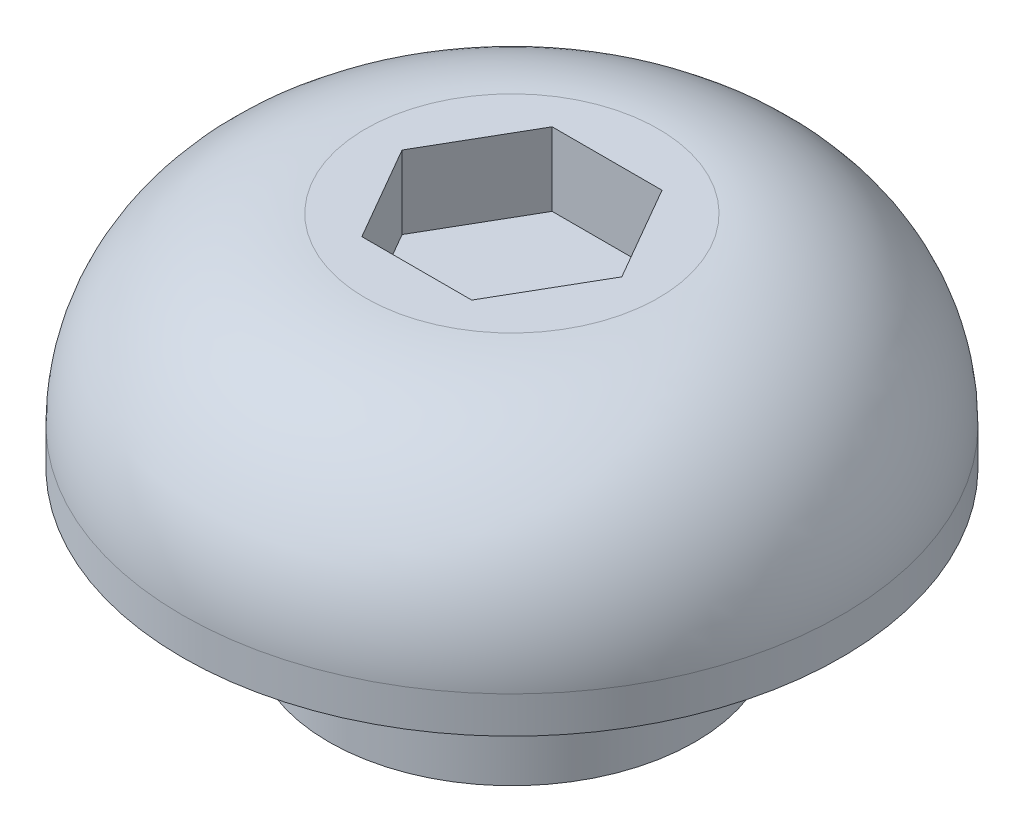
SolidWorks part; units mm, degrees
ref_plane "Front Plane" through (0, 0, 0) normal (0, 0, 1) x (1, 0, 0)
ref_plane "Top Plane" through (0, 0, 0) normal (0, 1, 0) x (1, 0, 0)
ref_plane "Right Plane" through (0, 0, 0) normal (1, 0, 0) x (0, 0, -1)
sketch "Sketch1" plane through (0, 0, 0) normal (0, 1, 0) x (1, 0, 0)
  circle A0 centre (0, 0) radius 4.5
  dimension "D1" = 9
extrude "Boss-Extrude1" add sketch "Sketch1" along normal blind 3
fillet "Fillet1" radius 2.5 1 edges at (0, 3, 4.5)
sketch "Sketch2" plane through (0, 3, 0) normal (0, 1, 0) x (1, 0, 0)
  line L1 (1.5, 0) -> (0.75, 1.299)
  line L2 (0.75, 1.299) -> (-0.75, 1.299)
  line L3 (-0.75, 1.299) -> (-1.5, 0)
  line L4 (-1.5, 0) -> (-0.75, -1.299)
  line L5 (-0.75, -1.299) -> (0.75, -1.299)
  line L6 (0.75, -1.299) -> (1.5, 0)
  circle A0 centre (0, 0) radius 1.299 construction
  point P1 (0, 1.299)
  dimension "D1" = 1.5
extrude "Cut-Extrude1" cut sketch "Sketch2" against normal blind 1
sketch "Sketch3" plane through (0, 0, 0) normal (0, -1, 0) x (-1, 0, 0)
  circle A0 centre (0, 0) radius 2.5
  dimension "D1" = 5
extrude "Boss-Extrude2" add sketch "Sketch3" along normal blind 2
